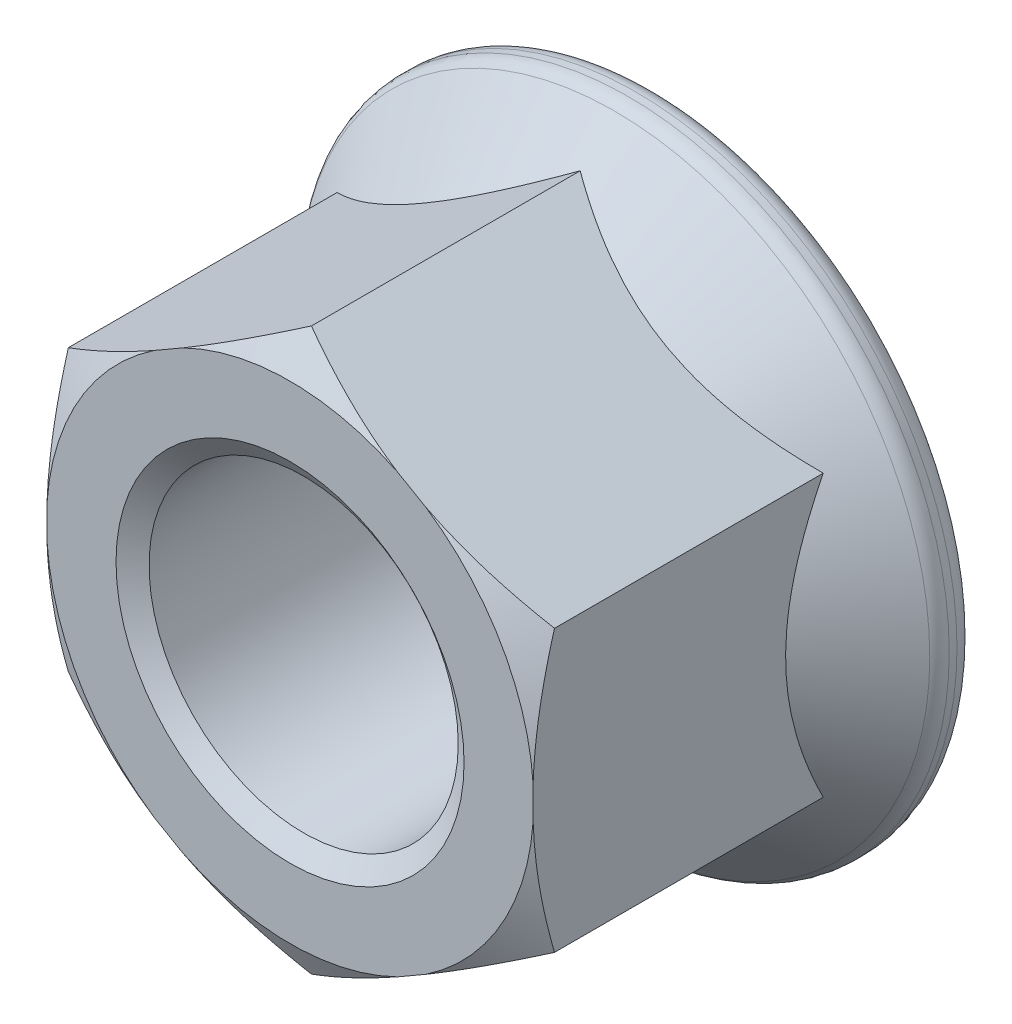
SolidWorks part; units mm, degrees
ref_plane "Front Plane" through (0, 0, 0) normal (0, 0, 1) x (1, 0, 0)
ref_plane "Top Plane" through (0, 0, 0) normal (0, 1, 0) x (1, 0, 0)
ref_plane "Right Plane" through (0, 0, 0) normal (1, 0, 0) x (0, 0, -1)
sketch "Sketch1" plane through (0, 0, 0) normal (1, 0, 0) x (0, -1, 0)
  line L1 (2.2732, 0) -> (3.1822, 0)
  line L5 (2.2732, 0) -> (2.0193, 0.1778)
  line L7 (3.6662, 3.7895) -> (4.1166, 4.2399)
  line L9 (3.937, 4.7751) -> (2.1972, 4.7751)
  line L10 (4.191, 4.4195) -> (4.191, 4.5211)
  line L11 (2.0193, 0.1778) -> (2.0193, 4.5211)
  line L13 (2.0193, 4.5211) -> (2.1972, 4.7751)
  line L14 (0, 0) -> (0, 4.7008) construction
  line L15 (3.6662, 3.7895) -> (3.6662, 0.2794)
  line L17 (3.1822, 0) -> (3.6662, 0.2794)
  arc A1 (4.1166, 4.2399) -> (4.191, 4.4195) centre (3.937, 4.4195) ccw
  arc A3 (4.191, 4.5211) -> (3.937, 4.7751) centre (3.937, 4.5211) ccw
  dimension "D10" = 0.254
  dimension "D1" = 4.0386
  dimension "D2" = 35
  dimension "D3" = 0.254
  dimension "D4" = 55
  dimension "D5" = 0.1778
  dimension "D6" = 4.7751
  dimension "D7" = 60
  dimension "D8" = 3.6662
  dimension "D9" = 0.2794
  dimension "D11" = 2.1717
  dimension "D12" = 0.1016
  dimension "D13" = 45
revolve "Revolve1" add sketch "Sketch1" angle 360 about L14
sketch "Sketch2" plane through (0, 0, 0) normal (0, 0, 1) x (1, 0, 0)
  line L1 (0, 3.6662) -> (-3.175, 1.8331)
  line L3 (3.175, 1.8331) -> (0, 3.6662)
  line L4 (3.175, -1.8331) -> (3.175, 1.8331)
  line L5 (0, -3.6662) -> (3.175, -1.8331)
  line L6 (-3.175, -1.8331) -> (0, -3.6662)
  line L7 (-3.175, 1.8331) -> (-3.175, -1.8331)
  circle A2 centre (0, 0) radius 3.7932
  dimension "D1" = 3.175
  dimension "D2" = 3.175
  dimension "D3" = 0.127
extrude "C-Ext Hex" cut sketch "Sketch2" against normal up to surface (3.7895 mm away)
